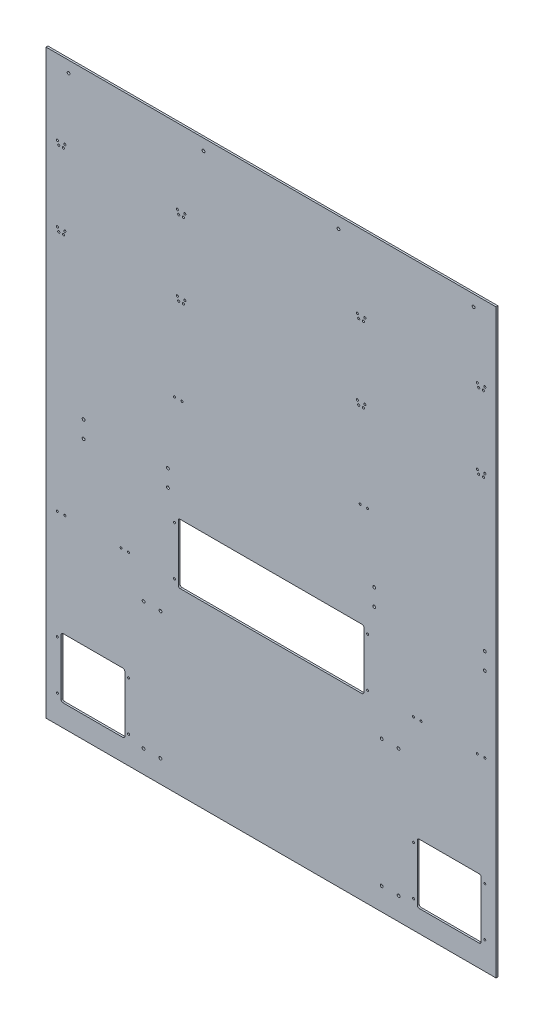
SolidWorks part; units mm, degrees
material "PC High Viscosity"
ref_plane "Front Plane" through (0, 0, 0) normal (0, 0, 1) x (1, 0, 0)
ref_plane "Top Plane" through (0, 0, 0) normal (0, 1, 0) x (1, 0, 0)
ref_plane "Right Plane" through (0, 0, 0) normal (1, 0, 0) x (0, 0, -1)
sketch "Sketch1" plane through (0, 0, 0) normal (0, 0, 1) x (1, 0, 0)
  line L1 (-762, -984.25) -> (762, -984.25)
  line L2 (-762, -984.25) -> (-762, 984.25)
  line L3 (-762, 984.25) -> (762, 984.25)
  line L4 (762, -984.25) -> (762, 984.25)
  line L5 (-762, -984.25) -> (762, 984.25) construction
  line L6 (-762, 984.25) -> (762, -984.25) construction
  point P0 (0, 0)
  dimension "D1" = 1524
  dimension "D2" = 1968.5
extrude "Boss-Extrude1" add sketch "Sketch1" along normal blind 6.35
sketch "Sketch2" plane through (0, 0, 6.35) normal (0, 0, 1) x (1, 0, 0)
  line L0 (-762, -984.25) -> (762, -984.25) construction
  line L1 (-314.325, -377.0122) -> (314.325, -377.0122)
  line L2 (-314.325, -377.0122) -> (-314.325, -173.8122)
  line L3 (-314.325, -173.8122) -> (314.325, -173.8122)
  line L4 (314.325, -377.0122) -> (314.325, -173.8122)
  line L5 (-314.325, -377.0122) -> (314.325, -173.8122) construction
  line L6 (-314.325, -173.8122) -> (314.325, -377.0122) construction
  point P0 (0, -275.4122)
  dimension "D1" = 628.65
  dimension "D2" = 607.2378
  dimension "D3" = 203.2
  dimension "D4" = 0
extrude "Cut-Extrude1" cut sketch "Sketch2" against normal through all
fillet "Fillet1" radius 6.35 4 edges at (314.325, -377.0122, 3.175) (314.325, -173.8122, 3.175) (-314.325, -173.8122, 3.175) (-314.325, -377.0122, 3.175)
sketch "Sketch3" plane through (0, 0, 6.35) normal (0, 0, 1) x (1, 0, 0)
  line L0 (-762, -984.25) -> (762, -984.25) construction
  line L1 (-711.2, -910.4122) -> (-495.3, -910.4122)
  line L2 (-711.2, -910.4122) -> (-711.2, -707.2122)
  line L3 (-711.2, -707.2122) -> (-495.3, -707.2122)
  line L4 (-495.3, -910.4122) -> (-495.3, -707.2122)
  line L5 (-711.2, -910.4122) -> (-495.3, -707.2122) construction
  line L6 (-711.2, -707.2122) -> (-495.3, -910.4122) construction
  line L8 (-762, 984.25) -> (-762, -984.25) construction
  point P0 (-603.25, -808.8122)
  dimension "D1" = 203.2
  dimension "D2" = 215.9
  dimension "D3" = 73.8378
  dimension "D4" = 50.8
extrude "Cut-Extrude2" cut sketch "Sketch3" against normal through all
sketch "Sketch4" plane through (0, 0, 6.35) normal (0, 0, 1) x (1, 0, 0)
  line L0 (762, -984.25) -> (762, 984.25) construction
  line L1 (495.3, -910.4122) -> (711.2, -910.4122)
  line L2 (495.3, -910.4122) -> (495.3, -707.2122)
  line L3 (495.3, -707.2122) -> (711.2, -707.2122)
  line L4 (711.2, -910.4122) -> (711.2, -707.2122)
  line L5 (495.3, -910.4122) -> (711.2, -707.2122) construction
  line L6 (495.3, -707.2122) -> (711.2, -910.4122) construction
  line L7 (-762, -984.25) -> (762, -984.25) construction
  point P0 (603.25, -808.8122)
  dimension "D1" = 215.9
  dimension "D2" = 203.2
  dimension "D3" = 50.8
  dimension "D4" = 73.8378
extrude "Cut-Extrude3" cut sketch "Sketch4" against normal blind 6.35
fillet "Fillet2" radius 6.35 8 edges at (711.2, -910.4122, 3.175) (711.2, -707.2122, 3.175) (495.3, -910.4122, 3.175) (495.3, -707.2122, 3.175) (-711.2, -707.2122, 3.175) (-495.3, -707.2122, 3.175) (-495.3, -910.4122, 3.175) (-711.2, -910.4122, 3.175)
sketch "Sketch5" plane through (0, 0, 6.35) normal (0, 0, 1) x (1, 0, 0)
  line L0 (-719.1375, 717.55) -> (-723.9, 730.25) construction
  line L1 (-723.9, 730.25) -> (-698.5, 730.25) construction
  line L2 (-698.5, 730.25) -> (-703.2625, 717.55) construction
  line L4 (-723.9, 730.25) -> (-703.2625, 717.55) construction
  line L5 (-698.5, 730.25) -> (-719.1375, 717.55) construction
  line L7 (-719.1375, 717.55) -> (-703.2625, 717.55) construction
  line L8 (762, 984.25) -> (-762, 984.25) construction
  circle A0 centre (-723.9, 730.25) radius 3.5719
  circle A1 centre (-698.5, 730.25) radius 3.5719
  circle A2 centre (-719.1375, 717.55) radius 3.5719
  circle A3 centre (-703.2625, 717.55) radius 3.5719
  point P9 (-711.2, 730.25)
  dimension "D1" = 7.1437
  dimension "D2" = 25.4
  dimension "D3" = 711.2
  dimension "D4" = 254
  dimension "D5" = 15.875
  dimension "D6" = 12.7
extrude "Cut-Extrude4" cut sketch "Sketch5" against normal through all
pattern_linear "LPattern1" count 2 spacing 406.4 along (1, 0, 0) count 2 spacing 254 along (0, -1, 0) of "Cut-Extrude4"
mirror "Mirror1" about plane through (0, 0, 0) normal (1, 0, 0) of "LPattern1", "Cut-Extrude4"
sketch "Sketch6" plane through (0, 0, 6.35) normal (0, 0, 1) x (1, 0, 0)
  line L0 (-762, 984.25) -> (-762, -984.25) construction
  line L1 (762, 984.25) -> (-762, 984.25) construction
  circle A0 centre (-685.8, 946.15) radius 4.7625
  dimension "D1" = 76.2
  dimension "D3" = 9.525
  dimension "D2" = 38.1
extrude "Cut-Extrude5" cut sketch "Sketch6" against normal through all
pattern_linear "LPattern2" count 4 spacing 457.2 along (1, 0, 0) of "Cut-Extrude5"
sketch "Sketch7" plane through (0, 0, 6.35) normal (0, 0, 1) x (1, 0, 0)
  line L0 (-711.2, -713.5622) -> (-711.2, -904.0622) construction
  line L1 (-495.3, -904.0622) -> (-495.3, -713.5622) construction
  line L2 (-704.85, -910.4122) -> (-501.65, -910.4122) construction
  line L3 (-501.65, -707.2122) -> (-704.85, -707.2122) construction
  line L5 (495.3, -713.5622) -> (495.3, -904.0622) construction
  line L6 (711.2, -904.0622) -> (711.2, -713.5622) construction
  line L7 (-314.325, -180.1622) -> (-314.325, -370.6622) construction
  line L8 (314.325, -370.6622) -> (314.325, -180.1622) construction
  line L9 (307.975, -173.8122) -> (-307.975, -173.8122) construction
  line L10 (-307.975, -377.0122) -> (307.975, -377.0122) construction
  circle A0 centre (-723.9, -726.2622) radius 3.3655
  circle A1 centre (-723.9, -891.3622) radius 3.3655
  circle A2 centre (-482.6, -726.2622) radius 3.3655
  circle A3 centre (-482.6, -891.3622) radius 3.3655
  circle A4 centre (482.6, -726.2622) radius 3.3655
  circle A5 centre (482.6, -891.3622) radius 3.3655
  circle A6 centre (723.9, -891.3622) radius 3.3655
  circle A7 centre (723.9, -726.2622) radius 3.3655
  circle A8 centre (-327.025, -192.8622) radius 3.3655
  circle A9 centre (-327.025, -357.9622) radius 3.3655
  circle A10 centre (327.025, -192.8622) radius 3.3655
  circle A11 centre (327.025, -357.9622) radius 3.3655
  circle A12 centre (-723.9, -357.9622) radius 3.3655
  circle A13 centre (-698.5, -357.9622) radius 3.3655
  circle A14 centre (-508, -357.9622) radius 3.3655
  circle A15 centre (-482.6, -357.9622) radius 3.3655
  circle A16 centre (482.6, -357.9622) radius 3.3655
  circle A17 centre (508, -357.9622) radius 3.3655
  circle A18 centre (698.5, -357.9622) radius 3.3655
  circle A19 centre (723.9, -357.9622) radius 3.3655
  circle A20 centre (-327.025, 175.4378) radius 3.3655
  circle A21 centre (-301.625, 175.4378) radius 3.3655
  circle A22 centre (301.625, 175.4378) radius 3.3655
  circle A23 centre (327.025, 175.4378) radius 3.3655
  dimension "D1" = 12.7
  dimension "D2" = 6.731
  dimension "D12" = 368.3
  dimension "D3" = 12.7
  dimension "D4" = 19.05
  dimension "D5" = 19.05
  dimension "D6" = 12.7
  dimension "D7" = 12.7
  dimension "D8" = 12.7
  dimension "D9" = 12.7
  dimension "D10" = 19.05
  dimension "D11" = 19.05
  dimension "D13" = 25.4
  dimension "D14" = 25.4
  dimension "D15" = 25.4
  dimension "D16" = 25.4
  dimension "D17" = 25.4
  dimension "D18" = 25.4
  dimension "D19" = 368.3
extrude "Cut-Extrude6" cut sketch "Sketch7" against normal through all
sketch "Sketch8" plane through (0, 0, 6.35) normal (0, 0, 1) x (1, 0, 0)
  line L0 (762, -984.25) -> (762, 984.25) construction
  line L2 (-762, -984.25) -> (762, -984.25) construction
  circle A2 centre (349.25, -44.45) radius 4.7625
  circle A3 centre (349.25, -101.6) radius 4.7625
  circle A4 centre (374.65, -908.05) radius 4.7625
  circle A5 centre (431.8, -908.05) radius 4.7625
  circle A6 centre (374.65, -476.25) radius 4.7625
  circle A7 centre (431.8, -476.25) radius 4.7625
  dimension "D1" = 9.525
  dimension "D2" = 939.8
  dimension "D3" = 412.75
  dimension "D4" = 387.35
  dimension "D5" = 57.15
  dimension "D6" = 57.15
  dimension "D8" = 76.2
  dimension "D9" = 508
extrude "Cut-Extrude7" cut sketch "Sketch8" against normal through all
mirror "Mirror2" about plane through (0, 0, 0) normal (1, 0, 0) of "Cut-Extrude7"
sketch "Sketch10" plane through (0, 0, 6.35) normal (0, 0, 1) x (1, 0, 0)
  line L0 (-762, -984.25) -> (762, -984.25) construction
  line L1 (762, -984.25) -> (762, 984.25) construction
  line L2 (-762, 984.25) -> (-762, -984.25) construction
  circle A0 centre (-635, -44.45) radius 4.7625
  circle A1 centre (-635, -101.6) radius 4.7625
  circle A2 centre (723.9, -44.45) radius 4.7625
  circle A3 centre (723.9, -101.6) radius 4.7625
  dimension "D1" = 939.8
  dimension "D2" = 9.525
  dimension "D3" = 57.15
  dimension "D4" = 38.1
  dimension "D5" = 127
extrude "Cut-Extrude8" cut sketch "Sketch10" against normal through all
